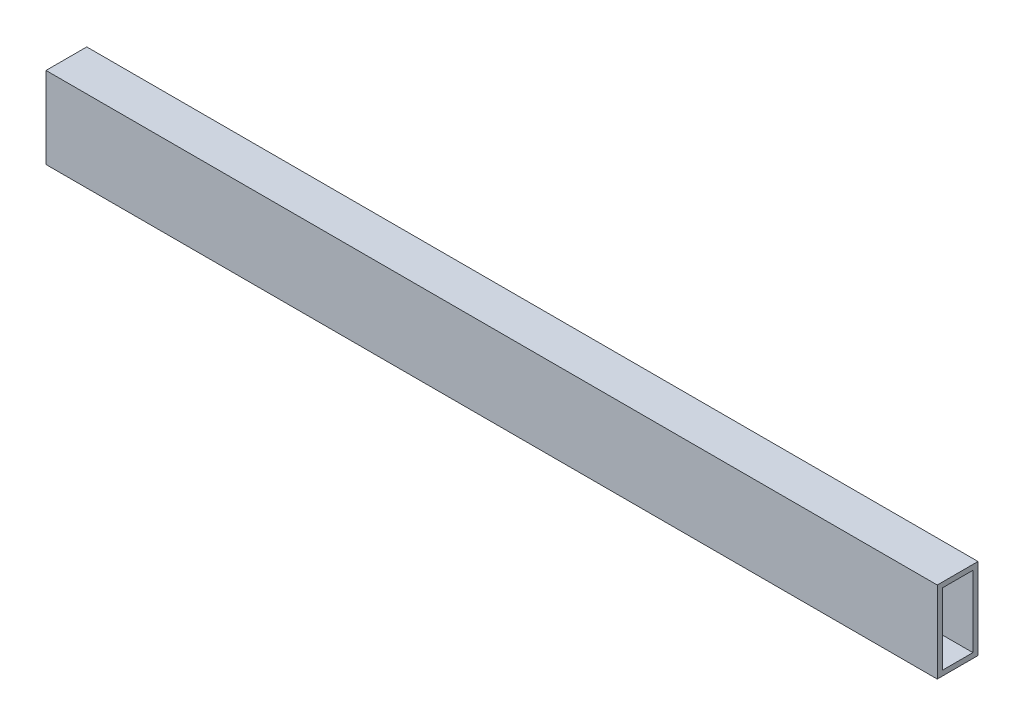
SolidWorks part; units mm, degrees
ref_plane "Front Plane" through (0, 0, 0) normal (0, 0, 1) x (1, 0, 0)
ref_plane "Top Plane" through (0, 0, 0) normal (0, 1, 0) x (1, 0, 0)
ref_plane "Right Plane" through (0, 0, 0) normal (1, 0, 0) x (0, 0, -1)
sketch "Sketch1" plane through (0, 0, 0) normal (1, 0, 0) x (0, 0, -1)
  line L1 (0, 0) -> (25.4, 0)
  line L2 (0, 0) -> (0, 50.8)
  line L3 (0, 50.8) -> (25.4, 50.8)
  line L4 (25.4, 0) -> (25.4, 50.8)
  line L5 (3.175, 47.625) -> (22.225, 47.625)
  line L6 (3.175, 47.625) -> (3.175, 3.175)
  line L7 (3.175, 3.175) -> (22.225, 3.175)
  line L8 (22.225, 47.625) -> (22.225, 3.175)
  dimension "D1" = 3.175
  dimension "D2" = 3.175
  dimension "D3" = 3.175
  dimension "D4" = 3.175
  dimension "D5" = 25.4
  dimension "D6" = 50.8
extrude "Boss-Extrude1" add sketch "Sketch1" along normal blind 555.625
